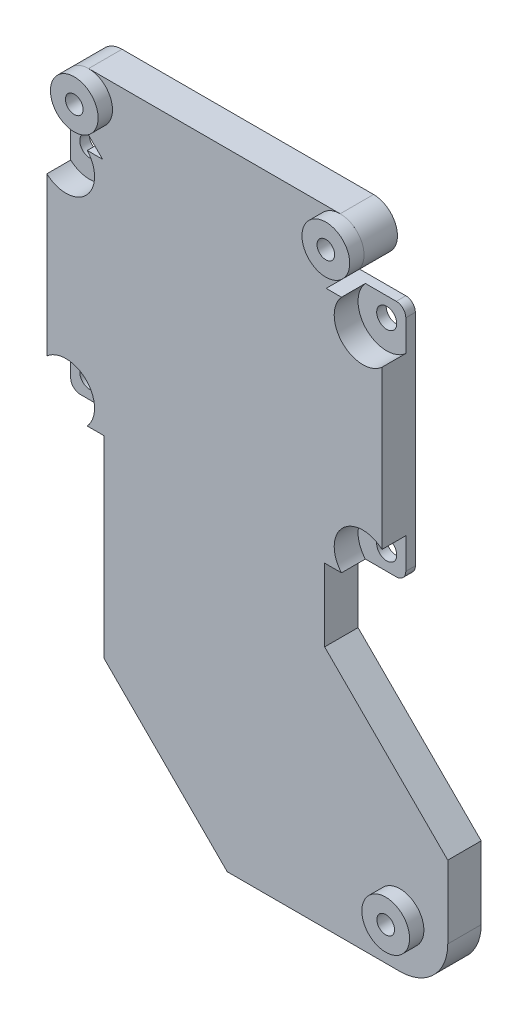
SolidWorks part; units mm, degrees
ref_plane "Front Plane" through (0, 0, 0) normal (0, 0, 1) x (1, 0, 0)
ref_plane "Top Plane" through (0, 0, 0) normal (0, 1, 0) x (1, 0, 0)
ref_plane "Right Plane" through (0, 0, 0) normal (1, 0, 0) x (0, 0, -1)
sketch "Sketch1" plane through (0, 0, 0) normal (0, 0, 1) x (1, 0, 0)
  line L1 (-68.2, 50) -> (-2, 50)
  line L2 (-70.2, 48) -> (-70.2, 2)
  line L3 (-68.2, 0) -> (-2, 0)
  line L4 (0, 48) -> (0, 2)
  arc A0 (-70.2, 2) -> (-68.2, 0) centre (-68.2, 2) ccw
  arc A1 (-2, 50) -> (0, 48) centre (-2, 48) cw
  arc A2 (-68.2, 50) -> (-70.2, 48) centre (-68.2, 48) ccw
  arc A3 (-2, 0) -> (0, 2) centre (-2, 2) ccw
  circle A4 centre (-66.2, 46) radius 2.1
  circle A5 centre (-4, 46) radius 2.1
  circle A6 centre (-4, 4) radius 2.1
  circle A7 centre (-66.2, 4) radius 2.1
  point P14 (0, 0)
  point P22 (0, 0)
  point P23 (0, 0)
  point P24 (0, 0)
  point P25 (0, 0)
  point P26 (-20.5612, 27.4351)
  point P27 (-36.9342, 10.9426)
  point P28 (-9.2558, 7.8838)
  point P29 (-75.0625, 52.8231)
  dimension "D2" = 4.2
  dimension "D3" = 62.2
  dimension "D4" = 42
  dimension "D5" = 4
  dimension "D6" = 4
  dimension "D7" = 4
  dimension "D8" = 4
extrude "Boss-Extrude1" add sketch "Sketch1" along normal blind 2
sketch "Sketch2" plane through (0, 0, 2) normal (0, 0, 1) x (1, 0, 0)
  line L8 (-68.2, 0) -> (-2, 0)
  line L9 (0, 2) -> (0, 48)
  line L10 (-2, 50) -> (-68.2, 50)
  line L11 (-70.2, 48) -> (-70.2, 2)
  line L12 (-61.7279, 0) -> (-8.4721, 0)
  line L13 (0, 8.4721) -> (0, 41.5279)
  line L14 (-8.4721, 50) -> (-61.7279, 50)
  line L15 (-70.2, 41.5279) -> (-70.2, 8.4721)
  arc A4 (-70.2, 41.5279) -> (-61.7279, 50) centre (-66.2, 46) ccw
  arc A5 (-8.4721, 50) -> (0, 41.5279) centre (-4, 46) ccw
  arc A6 (0, 8.4721) -> (-8.4721, 0) centre (-4, 4) ccw
  arc A7 (-61.7279, 0) -> (-70.2, 8.4721) centre (-66.2, 4) ccw
  arc A8 (-70.2, 2) -> (-68.2, 0) centre (-68.2, 2) ccw
  arc A9 (-2, 0) -> (0, 2) centre (-2, 2) ccw
  arc A10 (0, 48) -> (-2, 50) centre (-2, 48) ccw
  arc A11 (-68.2, 50) -> (-70.2, 48) centre (-68.2, 48) ccw
  dimension "D2" = 6
  dimension "D1" = 0
extrude "Boss-Extrude2" add sketch "Sketch2" along normal blind 5
sketch "Sketch3" plane through (0, 0, 7) normal (0, 0, 1) x (1, 0, 0)
  line L0 (-35.1, 50) -> (-35.1, 0) construction
  line L1 (-8.4721, 50) -> (-61.7279, 50) construction
  line L2 (-61.7279, 0) -> (-8.4721, 0) construction
  circle A0 centre (-61.45, 60) radius 1.85
  circle A1 centre (-8.75, 60) radius 1.85
  circle A2 centre (3.79, -56.2) radius 1.85
  circle A3 centre (-61.45, 60) radius 5
  circle A4 centre (-8.75, 60) radius 5
  circle A5 centre (3.79, -56.2) radius 5
  dimension "D3" = 3.7
  dimension "D6" = 10
  dimension "D1" = 52.7
  dimension "D2" = 10
  dimension "D4" = 116.2
  dimension "D5" = 12.54
extrude "Boss-Extrude3" add sketch "Sketch3" along normal blind 3
sketch "Sketch4" plane through (0, 0, 7) normal (0, 0, 1) x (1, 0, 0)
  line L0 (13.79, -56.2) -> (13.79, -40.995)
  line L1 (13.79, -40.995) -> (-12, -15.205)
  line L2 (-12, -15.205) -> (-12, 0)
  line L3 (-61.7279, 0) -> (-8.4721, 0) construction
  line L4 (-12, 0) -> (-58.2, 0)
  line L5 (-58.2, 0) -> (-58.2, -40.41)
  line L6 (3.79, -66.2) -> (-32.41, -66.2)
  line L7 (-32.41, -66.2) -> (-58.2, -40.41)
  line L8 (-70.2, 41.5279) -> (-70.2, 8.4721) construction
  line L9 (0, 8.4721) -> (0, 41.5279) construction
  line L10 (-64.9855, 56.4645) -> (-58.5211, 50)
  line L11 (-58.5211, 50) -> (-11.6789, 50)
  line L12 (-11.6789, 50) -> (-5.2145, 56.4645)
  line L13 (-8.75, 65) -> (-61.45, 65)
  line L14 (-8.4721, 50) -> (-61.7279, 50) construction
  line L15 (-2, 50) -> (-8.4721, 50) construction
  arc A0 (3.79, -66.2) -> (13.79, -56.2) centre (3.79, -56.2) ccw
  circle A1 centre (3.79, -56.2) radius 1.85
  circle A2 centre (-61.45, 60) radius 1.85
  circle A3 centre (-8.75, 60) radius 1.85
  arc A4 (-61.45, 65) -> (-64.9855, 56.4645) centre (-61.45, 60) ccw
  arc A5 (-5.2145, 56.4645) -> (-8.75, 65) centre (-8.75, 60) ccw
  circle A6 centre (-61.45, 60) radius 5 construction
  circle A7 centre (-8.75, 60) radius 5 construction
  point P31 (-8.75, 57.5901)
  dimension "D1" = 20
  dimension "D6" = 3.7
  dimension "D7" = 10
  dimension "D2" = 45
  dimension "D3" = 12
  dimension "D4" = 12
  dimension "D5" = 52.7
  dimension "D8" = 45
  dimension "D9" = 45
extrude "Boss-Extrude4" add sketch "Sketch4" against normal up to surface (7 mm away) up to face at (-35.1, 25, 0)
equation "\"D6@Sketch1\"=\"D5@Sketch1\""
equation "\"D7@Sketch1\"=\"D5@Sketch1\""
equation "\"D8@Sketch1\"=\"D5@Sketch1\""
equation "\"D4@Sketch4\"=\"D3@Sketch4\""
